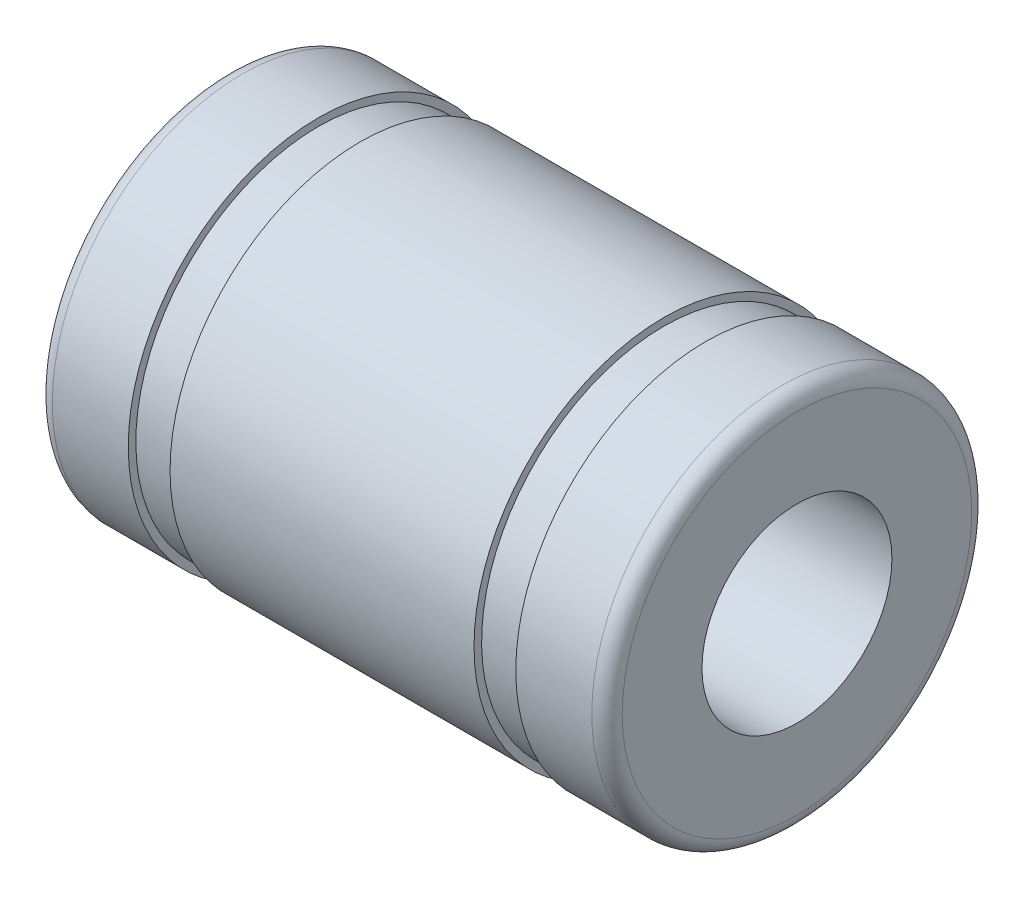
SolidWorks part; units mm, degrees
ref_plane "Front Plane" through (0, 0, 0) normal (0, 0, 1) x (1, 0, 0)
ref_plane "Top Plane" through (0, 0, 0) normal (0, 1, 0) x (1, 0, 0)
ref_plane "Right Plane" through (0, 0, 0) normal (1, 0, 0) x (0, 0, -1)
sketch "Sketch1" plane through (0, 0, 0) normal (0, 0, 1) x (1, 0, 0)
  line L0 (0, 0) -> (15, 0) construction
  line L2 (15, 2.5) -> (0, 2.5)
  line L3 (15, 2.5) -> (15, 5)
  line L4 (15, 5) -> (0, 5)
  line L5 (0, 2.5) -> (0, 5)
  dimension "D" = 10
  dimension "DR_s" = 5
  dimension "L" = 15
revolve "Revolve1" add sketch "Sketch1" angle 360 about L0
fillet "Fillet1" radius 0.4 2 edges at (0, 0, 5) (15, 0, 5)
sketch "Sketch2" plane through (0, 0, 0) normal (0, 0, 1) x (1, 0, 0)
  line L0 (15, 0) -> (0, 0) construction
  line L2 (7.5, 5) -> (7.5, 0) construction
  line L6 (11.5, 5) -> (12.6, 5)
  line L7 (11.5, 5) -> (11.5, 4.8)
  line L8 (11.5, 4.8) -> (12.6, 4.8)
  line L9 (12.6, 5) -> (12.6, 4.8)
  line L10 (2.4, 5) -> (3.5, 5)
  line L11 (2.4, 5) -> (2.4, 4.8)
  line L12 (2.4, 4.8) -> (3.5, 4.8)
  line L13 (3.5, 5) -> (3.5, 4.8)
  dimension "D1." = 9.6
  dimension "B" = 8
  dimension "W" = 1.1
  dimension "L" = 15
  dimension "D" = 10
revolve "Cut-Revolve1" cut sketch "Sketch2" angle 360 about L0
sketch "Sketch5" [suppressed] plane through (0, 0, 0) normal (0, 0, 1) x (1, 0, 0)
  line L0 (0, 0) -> (16, 0) construction
  line L1 (7.6127, 6) -> (8.3873, 6)
  line L2 (8, 6) -> (8, 0) construction
  arc A0 (7.6127, 6) -> (8.3873, 6) centre (8, 6.1) ccw
  dimension "R" = 0.4
  dimension "L" = 15
  dimension "D" = 10
  dimension "F_s" = 0.3
revolve "Cut-Revolve2" [suppressed] cut sketch "Sketch5" angle 360 about L0
sketch "Sketch6" [suppressed] plane through (0, 0, 0) normal (0, 0, 1) x (1, 0, 0)
  line L0 (0, 0) -> (34, 0) construction
  line L2 (34, 5) -> (5, 5)
  line L3 (34, 5) -> (34, 9.5)
  line L4 (34, 9.5) -> (5, 9.5)
  line L5 (5, 5) -> (5, 9.5)
  dimension "D" = 10
  dimension "DR_s" = 5
  dimension "L1" = 29
  dimension "V" = 5
revolve "Revolve2" [suppressed] add sketch "Sketch6" angle 360 about L0
fillet "Fillet3" [suppressed] radius 0.4
sketch "Sketch7" [suppressed] plane through (0, 0, 0) normal (0, 0, 1) x (1, 0, 0)
  line L0 (15, 0) -> (0, 0) construction
  line L2 (5, 9.5) -> (5, 0) construction
  line L6 (14.7, 9.5) -> (15.8, 9.5)
  line L7 (14.7, 9.5) -> (14.7, 9)
  line L8 (14.7, 9) -> (15.8, 9)
  line L9 (15.8, 9.5) -> (15.8, 9)
  line L10 (-5.8, 9.5) -> (-4.7, 9.5)
  line L11 (-5.8, 9.5) -> (-5.8, 9)
  line L12 (-5.8, 9) -> (-4.7, 9)
  line L13 (-4.7, 9.5) -> (-4.7, 9)
  dimension "D1." = 9.6
  dimension "B" = 8
  dimension "W" = 1.1
  dimension "L" = 15
  dimension "D" = 10
  dimension "KSS_2" = 7.5
revolve "Cut-Revolve3" [suppressed] cut sketch "Sketch7" angle 360 about L0
sketch "Sketch4" [suppressed] plane through (0, 0, 0) normal (0, 0, 1) x (1, 0, 0)
  line L0 (0, 0) -> (39, 0) construction
  line L3 (34, 9.5) -> (39, 9.5)
  line L4 (34, 9.5) -> (34, 5)
  line L5 (34, 5) -> (39, 5)
  line L6 (39, 9.5) -> (39, 5)
  line L7 (0, 9.5) -> (5, 9.5)
  line L8 (0, 9.5) -> (0, 5)
  line L9 (0, 5) -> (5, 5)
  line L10 (5, 9.5) -> (5, 5)
  dimension "V" = 5
  dimension "L1" = 29
  dimension "L" = 15
  dimension "D" = 10
  dimension "DR_S" = 5
revolve "Revolve3" [suppressed] add sketch "Sketch4" angle 360 about L0
equation "\"KSS_2@Sketch7\" = \"L@Sketch1\" / 2"
